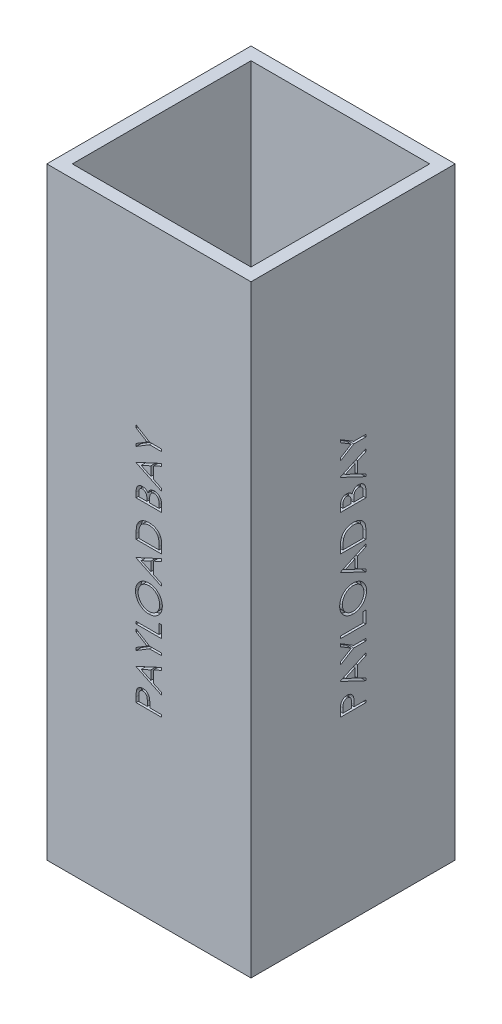
SolidWorks part; units mm, degrees
material "PVC Rigid"
ref_plane "Front Plane" through (0, 0, 0) normal (0, 0, 1) x (1, 0, 0)
ref_plane "Top Plane" through (0, 0, 0) normal (0, 1, 0) x (1, 0, 0)
ref_plane "Right Plane" through (0, 0, 0) normal (1, 0, 0) x (0, 0, -1)
sketch "Sketch1" plane through (0, 0, 0) normal (0, 1, 0) x (1, 0, 0)
  line L1 (-50.8, -50.8) -> (50.8, -50.8)
  line L2 (-50.8, -50.8) -> (-50.8, 50.8)
  line L3 (-50.8, 50.8) -> (50.8, 50.8)
  line L4 (50.8, -50.8) -> (50.8, 50.8)
  line L5 (-50.8, -50.8) -> (50.8, 50.8) construction
  line L6 (-50.8, 50.8) -> (50.8, -50.8) construction
  line L7 (-44.45, -44.45) -> (44.45, -44.45)
  line L8 (-44.45, -44.45) -> (-44.45, 44.45)
  line L9 (-44.45, 44.45) -> (44.45, 44.45)
  line L10 (44.45, -44.45) -> (44.45, 44.45)
  line L11 (-44.45, -44.45) -> (44.45, 44.45) construction
  line L12 (-44.45, 44.45) -> (44.45, -44.45) construction
  point P0 (0, 0)
  point P6 (0, 0)
  dimension "D1" = 101.6
  dimension "D2" = 101.6
  dimension "D3" = 88.9
extrude "Boss-Extrude1" add sketch "Sketch1" along normal blind 300
sketch "Sketch6" plane through (-50.8, 0, 0) normal (-1, 0, 0) x (0, 0, 1)
  line L0 (6.35, 0) -> (6.35, 300) construction
  line L1 (-50.8, 0) -> (50.8, 0) construction
  line L2 (-50.8, 300) -> (50.8, 300) construction
  line L3 (-50.8, 300) -> (-50.8, 0) construction
  text T0 "PAYLOAD BAY" font "Century Gothic" height in points 48
  dimension "D1" = 57.15
extrude "Cut-Extrude1" cut sketch "Sketch6" against normal blind 2.54
sketch "Sketch7" plane through (0, 0, 0) normal (0, 0, 1) x (1, 0, 0)
  line L0 (0, 0) -> (0, 300) construction
  line L1 (-50.8, 300) -> (50.8, 300) construction
pattern_circular "CirPattern1" count 4 over 360 about axis through (0, 0, 0) along (0, 1, 0) of "Cut-Extrude1"
